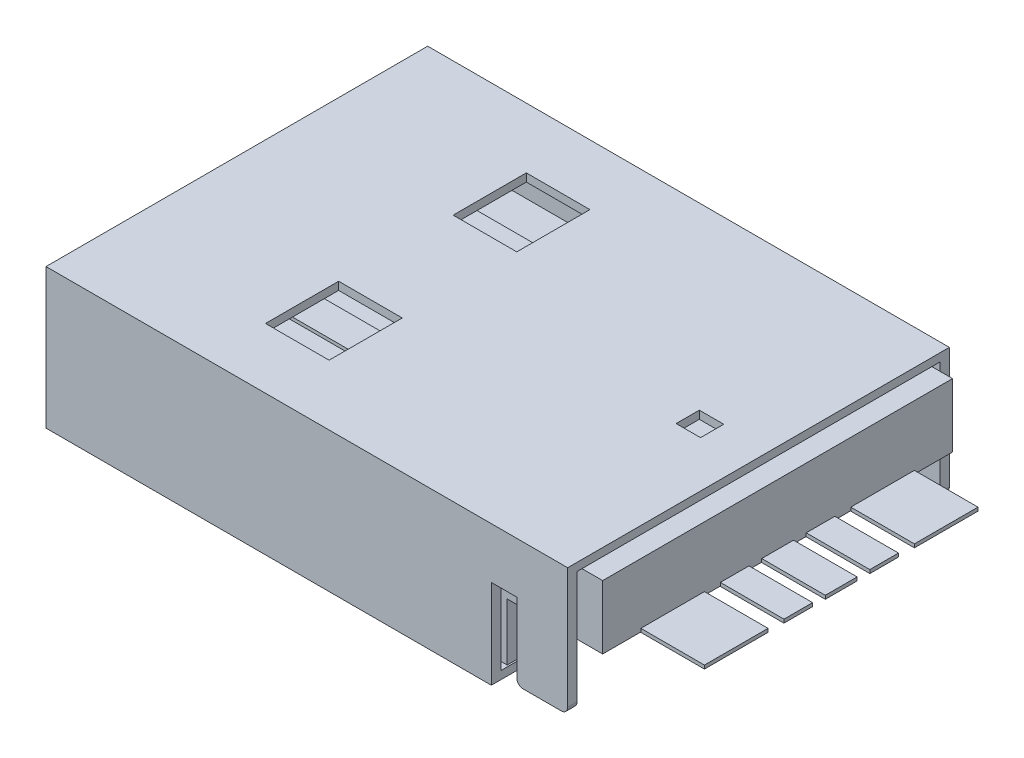
SolidWorks part; units mm, degrees
ref_plane "前视基准面" through (0, 0, 0) normal (0, 0, 1) x (1, 0, 0)
ref_plane "上视基准面" through (0, 0, 0) normal (0, 1, 0) x (1, 0, 0)
ref_plane "右视基准面" through (0, 0, 0) normal (1, 0, 0) x (0, 0, -1)
sketch "草图2" plane through (0, 0, 0) normal (0, 0, 1) x (1, 0, 0)
  line L0 (0, 0) -> (-14, 0)
  line L1 (-14, 0) -> (-14, 2)
  line L2 (-14, 2) -> (-5, 2)
  line L3 (-5, 2) -> (-5, 3.8)
  line L4 (-5, 3.8) -> (3, 3.8)
  line L5 (3, 3.8) -> (3, 1.8)
  line L6 (3, 1.8) -> (0, 1.8)
  line L7 (0, 1.8) -> (0, 0)
  dimension "D1" = 14
  dimension "D2" = 2
  dimension "D3" = 9
  dimension "D4" = 17
  dimension "D5" = 2
  dimension "D6" = 3.8
extrude "凸台-拉伸1" add sketch "草图2" along normal blind 11
sketch "草图3" plane through (0, 2, 0) normal (0, 1, 0) x (1, 0, 0)
  line L0 (-14, -5.5) -> (-5.8182, -5.5) construction
  line L1 (-14, -11) -> (-14, 0) construction
  line L2 (-5, -11) -> (-14, -11) construction
  line L3 (-13, -7) -> (-9, -7)
  line L4 (-13, -7) -> (-13, -6)
  line L5 (-13, -6) -> (-9, -6)
  line L6 (-9, -7) -> (-9, -6)
  line L7 (-13, -9.8) -> (-9, -9.8)
  line L8 (-13, -9.8) -> (-13, -7.8)
  line L9 (-13, -7.8) -> (-9, -7.8)
  line L10 (-9, -9.8) -> (-9, -7.8)
  line L11 (-13, -5) -> (-9, -5)
  line L12 (-9, -4) -> (-9, -5)
  line L13 (-13, -4) -> (-9, -4)
  line L14 (-13, -4) -> (-13, -5)
  line L15 (-13, -3.2) -> (-9, -3.2)
  line L16 (-9, -1.2) -> (-9, -3.2)
  line L17 (-13, -1.2) -> (-9, -1.2)
  line L18 (-13, -1.2) -> (-13, -3.2)
  dimension "D1" = 2
  dimension "D2" = 4
  dimension "D3" = 1
  dimension "D4" = 1
  dimension "D5" = 5
  dimension "D6" = 3.2
extrude "凸台-拉伸2" add sketch "草图3" along normal blind 0.1
ref_plane "基准面1" through (0, 0, 5.5) normal (0, 0, 1) x (1, 0, 0)
sketch "草图5" plane through (0, 2, 0) normal (0, 1, 0) x (1, 0, 0)
  line L0 (-2.2, -5.5) -> (2.2, -5.5) construction
  line L6 (-8.7594, -4.8) -> (-4.0524, -4.8)
  line L7 (-8.7594, -4.8) -> (-8.7594, -6.2)
  line L12 (-8.7594, -6.2) -> (-4.0524, -6.2)
  line L13 (-4.0524, -4.8) -> (-4.0524, -6.2)
  line L14 (-8.7594, -4.8) -> (-4.0524, -6.2) construction
  line L15 (-8.7594, -6.2) -> (-4.0524, -4.8) construction
  point P0 (-6.6179, -5.5)
  point P1 (-6.4059, -5.5)
  point P10 (-6.4059, -5.5)
  dimension "D1" = 1.4
extrude "切除-拉伸2" cut sketch "草图5" against normal through all and the other way through all
sketch "草图4" plane through (0, 0, 5.5) normal (0, 0, 1) x (1, 0, 0)
  line L7 (-8.4864, 0.9775) -> (-7.5448, 2.5523)
  line L8 (-7.5448, 2.5523) -> (-6.9184, 2.5523)
  line L9 (-6.9184, 2.5523) -> (-4.0524, 0.8388)
  line L10 (-4.0524, 0) -> (-4.0524, 3.8) construction
  line L11 (-4.0524, 0.8388) -> (-4.0524, 0.5856)
  line L12 (-4.0524, 0.5856) -> (-6.9238, 2.3024)
  line L13 (-6.9238, 2.3024) -> (-7.4567, 2.3024)
  line L14 (-7.4567, 2.3024) -> (-8.3177, 0.8622)
  line L15 (-8.3177, 0.8622) -> (-8.4864, 0.9775)
extrude "凸台-拉伸3" add sketch "草图4" along normal mid plane 1
fillet "圆角1" radius 0.6 4 edges at (-6.9238, 2.3024, 5.5) (-7.4567, 2.3024, 5.5) (-6.9184, 2.5523, 5.5) (-7.5448, 2.5523, 5.5)
sketch "草图6" plane through (0, 1.8, 0) normal (0, -1, 0) x (1, 0, 0)
  line L0 (0, 5.5) -> (5.3971, 5.5) construction
  line L1 (0, 11) -> (0, 0) construction
  line L2 (5, 4.6) -> (5, 3.7)
  line L3 (0, 7.8) -> (5, 7.8)
  line L4 (0, 7.8) -> (0, 9.8)
  line L5 (0, 9.8) -> (5, 9.8)
  line L6 (5, 7.8) -> (5, 9.8)
  line L7 (0, 6.4) -> (5, 6.4)
  line L8 (0, 6.4) -> (0, 7.3)
  line L9 (0, 7.3) -> (5, 7.3)
  line L10 (5, 6.4) -> (5, 7.3)
  line L11 (0, 3.7) -> (5, 3.7)
  line L12 (0, 4.6) -> (0, 3.7)
  line L13 (0, 4.6) -> (5, 4.6)
  line L14 (5, 3.2) -> (5, 1.2)
  line L15 (0, 1.2) -> (5, 1.2)
  line L16 (0, 3.2) -> (0, 1.2)
  line L17 (0, 3.2) -> (5, 3.2)
  line L18 (0, 11) -> (0, 0) construction
  line L19 (0, 5) -> (5, 5)
  line L20 (0, 5) -> (0, 6)
  line L21 (0, 6) -> (5, 6)
  line L22 (5, 5) -> (5, 6)
  dimension "D1" = 2
  dimension "D2" = 5
  dimension "D3" = 0.9
  dimension "D4" = 8.6
  dimension "D5" = 3.6
  dimension "D6" = 1
extrude "凸台-拉伸4" add sketch "草图6" against normal blind 0.1 and the other way blind 0.01
fillet "圆角2" radius 0.4 1 edges at (-14, 2, 5.5)
sketch "草图8" plane through (-14, 0, 0) normal (-1, 0, 0) x (0, 0, 1)
  line L0 (-0.2, 1.9) -> (-0.5, 1.9) construction
  line L1 (-0.2, -0.05) -> (11.2, -0.05)
  line L2 (-0.2, -0.05) -> (-0.2, 3.85)
  line L3 (-0.2, 3.85) -> (11.2, 3.85)
  line L4 (11.2, -0.05) -> (11.2, 3.85)
  line L5 (-0.5, -0.3) -> (11.5, -0.3)
  line L6 (-0.5, -0.3) -> (-0.5, 4.1)
  line L7 (-0.5, 4.1) -> (11.5, 4.1)
  line L8 (11.5, -0.3) -> (11.5, 4.1)
  line L9 (5.5, 4.1) -> (5.5, 3.8) construction
  line L10 (6.2, 3.8) -> (4.8, 3.8) construction
  line L12 (11, 3.8) -> (6.2, 3.8) construction
  line L13 (11, 0) -> (0, 0) construction
  dimension "D1" = 12
  dimension "D2" = 4.4
  dimension "D3" = 0.05
  dimension "D4" = 0.05
  dimension "D5" = 0.3
  dimension "D6" = 0.3
extrude "凸台-拉伸5" add sketch "草图8" against normal blind 16.4
sketch "草图9" plane through (0, 4.1, 0) normal (0, 1, 0) x (1, 0, 0)
  line L0 (2.4, -5.5) -> (-14, -5.5) construction
  line L1 (2.4, -11.5) -> (2.4, 0.5) construction
  line L2 (-14, -11.5) -> (-14, 0.5) construction
  line L3 (-7, -1.4) -> (-7, -3.7)
  line L4 (-7, -9.6) -> (-9, -9.6)
  line L5 (-7, -9.6) -> (-7, -7.3)
  line L6 (-7, -7.3) -> (-9, -7.3)
  line L7 (-9, -9.6) -> (-9, -7.3)
  line L8 (0.9471, -5.8703) -> (0.1796, -5.8703)
  line L9 (0.9471, -5.8703) -> (0.9471, -5.1405)
  line L10 (0.9471, -5.1405) -> (0.1796, -5.1405)
  line L11 (0.1796, -5.8703) -> (0.1796, -5.1405)
  line L12 (-7, -3.7) -> (-9, -3.7)
  line L13 (-9, -1.4) -> (-9, -3.7)
  line L14 (-7, -1.4) -> (-9, -1.4)
  dimension "D1" = 3.6
  dimension "D2" = 8.2
  dimension "D3" = 2
  dimension "D4" = 5
extrude "切除-拉伸5" cut sketch "草图9" against normal up to next (0.25 mm away)
sketch "草图12" plane through (0, -0.3, 0) normal (0, -1, 0) x (1, 0, 0)
  line L1 (-7, 9.6) -> (-9, 9.6)
  line L2 (-7, 9.6) -> (-7, 7.3)
  line L3 (-7, 7.3) -> (-9, 7.3)
  line L4 (-9, 9.6) -> (-9, 7.3)
  line L5 (-7, 3.7) -> (-9, 3.7)
  line L6 (-7, 3.7) -> (-7, 1.4)
  line L7 (-7, 1.4) -> (-9, 1.4)
  line L8 (-9, 3.7) -> (-9, 1.4)
extrude "切除-拉伸6" cut sketch "草图12" against normal up to next (0.25 mm away)
sketch "草图13" plane through (0, 0, 11.5) normal (0, 0, 1) x (1, 0, 0)
  line L0 (2.4, 0.1) -> (0.8, 0.1)
  line L1 (2.4, -0.05) -> (2.4, 3.85) construction
  line L2 (0.8, 0.1) -> (0.8, 2.5)
  line L3 (0.8, 2.5) -> (0, 2.5)
  line L4 (0, 2.5) -> (0, -0.7818)
  line L5 (0, -0.7818) -> (2.4, -0.7818)
  line L6 (2.4, -0.7818) -> (2.4, 0.1)
  line L7 (2.4, 4.1) -> (-14, 4.1) construction
  line L8 (0, 1.79) -> (0, 1.8) construction
  dimension "D1" = 4
  dimension "D2" = 1.6
  dimension "D3" = 1.6
extrude "切除-拉伸7" cut sketch "草图13" against normal through all both and the other way through all
fillet "圆角4" radius 0.2 4 edges at (2.4, 0.1, 11.35) (0.8, 0.1, 11.35) (2.4, 0.1, -0.35) (0.8, 0.1, -0.35)
